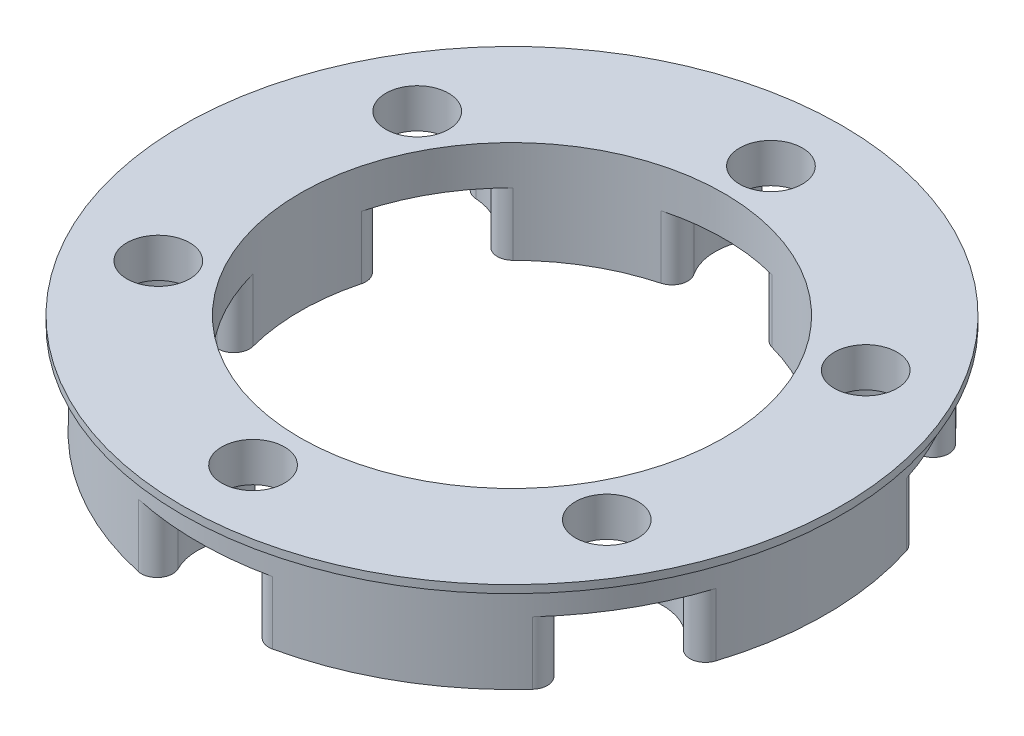
SolidWorks part; units mm, degrees
ref_plane "Front Plane" through (0, 0, 0) normal (0, 0, 1) x (1, 0, 0)
ref_plane "Top Plane" through (0, 0, 0) normal (0, 1, 0) x (1, 0, 0)
ref_plane "Right Plane" through (0, 0, 0) normal (1, 0, 0) x (0, 0, -1)
sketch "Sketch1" plane through (0, 0, 0) normal (0, 1, 0) x (1, 0, 0)
  circle A0 centre (0, 0) radius 20
  circle A1 centre (0, 0) radius 13.5
  dimension "D1" = 40
  dimension "D2" = 27
extrude "Boss-Extrude1" add sketch "Sketch1" along normal blind 6
sketch "Sketch2" plane through (0, 6, 0) normal (0, 1, 0) x (1, 0, 0)
  circle A0 centre (0, 16.5) radius 2
  dimension "D1" = 16.5
  dimension "D2" = 4
extrude "Cut-Extrude1" cut sketch "Sketch2" against normal through all
sketch "Sketch3" plane through (0, 0, 0) normal (0, 1, 0) x (1, 0, 0)
  circle A0 centre (0, 16.5) radius 3.55
  dimension "D1" = 7.1
extrude "Cut-Extrude4" cut sketch "Sketch3" along normal blind 4
fillet "Fillet1" radius 1 4 edges at (0.6536, 2, -19.9893) (-0.6536, 2, -19.9893) (1.7134, 2, -13.3908) (-1.7134, 2, -13.3908)
pattern_circular "CirPattern2" count 6 over 360 about axis through (0, 0, 0) along (0, 1, 0) of "Cut-Extrude1", "Cut-Extrude4", "Fillet1"
sketch "Sketch4" plane through (0, 6, 0) normal (0, 1, 0) x (1, 0, 0)
  circle A0 centre (0, 0) radius 21
  circle A1 centre (0, 0) radius 20 construction
  circle A2 centre (-14.2894, 8.25) radius 2 construction
  circle A3 centre (14.2894, 8.25) radius 2 construction
  circle A4 centre (14.2894, -8.25) radius 2 construction
  circle A5 centre (0, -16.5) radius 2 construction
  circle A6 centre (0, 0) radius 13.5 construction
  circle A7 centre (-14.2894, -8.25) radius 2 construction
  circle A8 centre (0, 16.5) radius 2 construction
  circle A9 centre (14.2894, 8.25) radius 2
  circle A10 centre (14.2894, -8.25) radius 2
  circle A11 centre (0, -16.5) radius 2
  circle A12 centre (0, 0) radius 13.5
  circle A13 centre (-14.2894, -8.25) radius 2
  circle A14 centre (-14.2894, 8.25) radius 2
  circle A15 centre (0, 16.5) radius 2
  dimension "D1" = 1
extrude "Boss-Extrude3" add sketch "Sketch4" along normal blind 0.5
